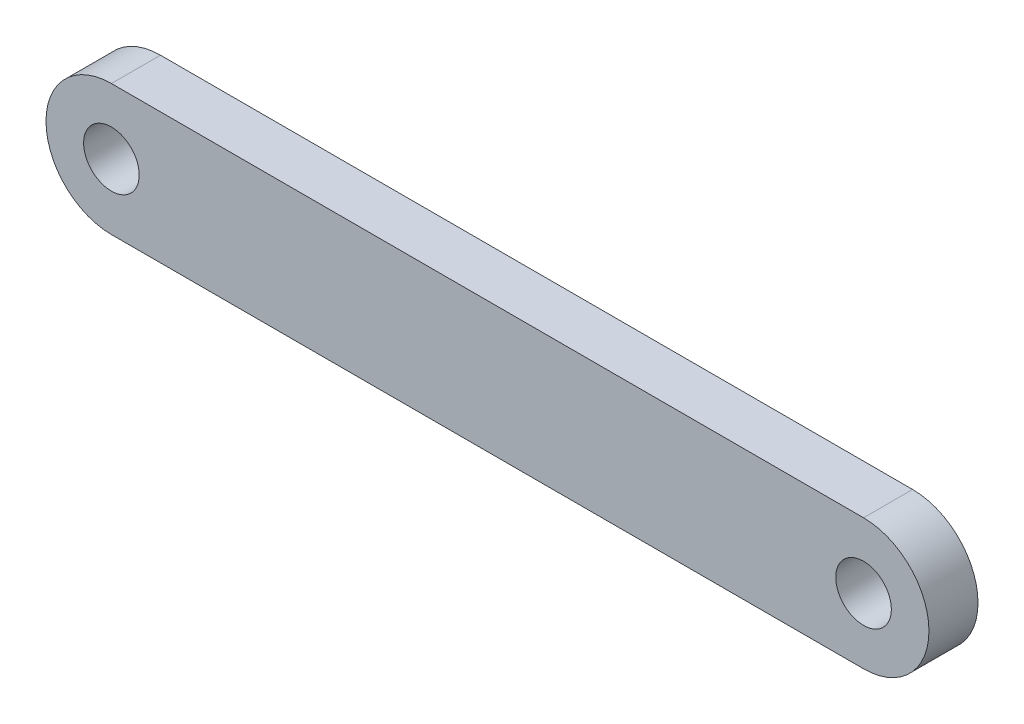
SolidWorks part; units mm, degrees
ref_plane "Plan de face" through (0, 0, 0) normal (0, 0, 1) x (1, 0, 0)
ref_plane "Plan de dessus" through (0, 0, 0) normal (0, 1, 0) x (1, 0, 0)
ref_plane "Plan de droite" through (0, 0, 0) normal (1, 0, 0) x (0, 0, -1)
sketch "Esquisse1" plane through (0, 0, 0) normal (0, 0, 1) x (1, 0, 0)
  line L0 (4, 8) -> (4, 0) construction
  line L1 (0, 0) -> (54, 0) construction
  line L2 (0, 0) -> (0, 8) construction
  line L3 (0, 8) -> (54, 8) construction
  line L4 (54, 0) -> (54, 8) construction
  line L5 (50, 8) -> (50, 0) construction
  line L6 (50, 8) -> (4, 8)
  line L7 (4, 0) -> (50, 0)
  arc A0 (4, 0) -> (4, 8) centre (4, 4) cw
  arc A1 (50, 8) -> (50, 0) centre (50, 4) cw
  circle A2 centre (4, 4) radius 1.7
  circle A3 centre (50, 4) radius 1.7
  dimension "D2" = 3.4
  dimension "D1" = 8
  dimension "D3" = 54
extrude "Boss.-Extru.1" add sketch "Esquisse1" along normal blind 3
